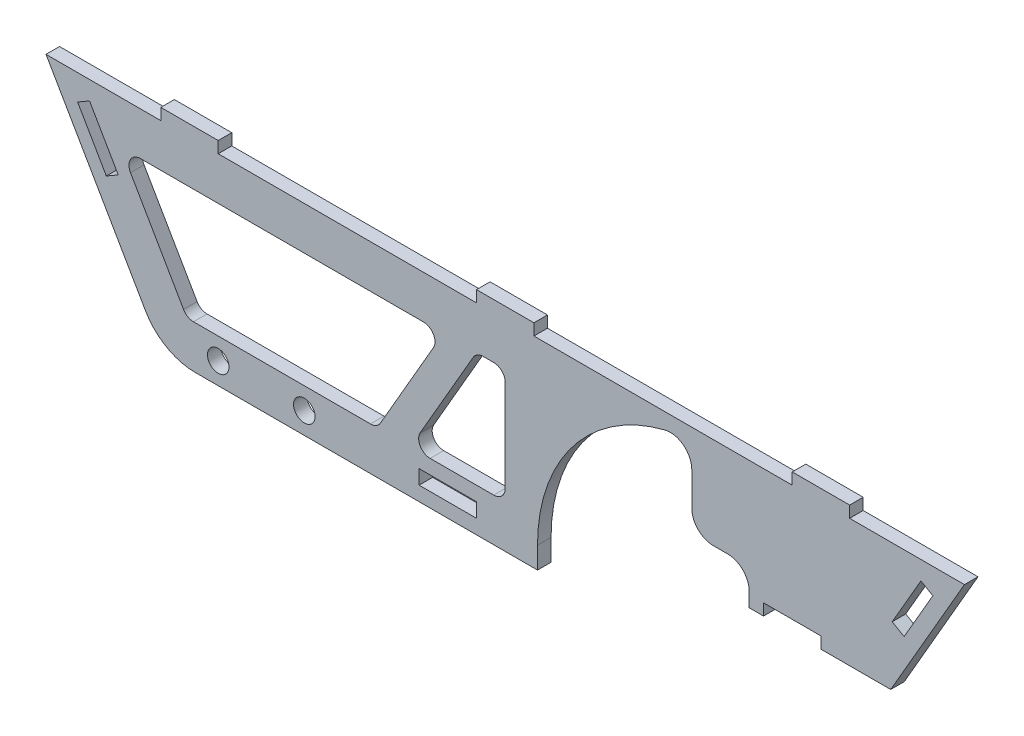
SolidWorks part; units mm, degrees
ref_plane "Front Plane" through (0, 0, 0) normal (0, 0, 1) x (1, 0, 0)
ref_plane "Top Plane" through (0, 0, 0) normal (0, 1, 0) x (1, 0, 0)
ref_plane "Right Plane" through (0, 0, 0) normal (1, 0, 0) x (0, 0, -1)
sketch "Sketch1" plane through (0, 0, 0) normal (0, 0, 1) x (1, 0, 0)
  line L0 (-101.6, 22.225) -> (-75.9368, -22.225)
  line L1 (-101.6, -22.225) -> (-75.9368, -22.225) construction
  line L2 (-101.6, -22.225) -> (-101.6, 22.225) construction
  line L3 (-101.6, 22.225) -> (101.6, 22.225)
  line L4 (101.6, -22.225) -> (101.6, 22.225) construction
  line L5 (-101.6, -22.225) -> (101.6, 22.225) construction
  line L6 (-101.6, 22.225) -> (101.6, -22.225) construction
  line L7 (0, 22.225) -> (0, -25.4) construction
  line L8 (-75.9368, -22.225) -> (101.6, -22.225)
  line L9 (-9.7602, 13.1434) -> (-32.8669, -26.8786) construction
  line L10 (9.7602, 13.1434) -> (32.8669, -26.8786) construction
  line L11 (101.6, 22.225) -> (75.9368, -22.225)
  line L12 (-13.6823, 12.7) -> (-28.347, -12.7)
  line L13 (0, 12.7) -> (0, -12.7)
  line L14 (-6.35, 12.7) -> (-21.0147, -12.7)
  line L15 (-10.4636, 11.9251) -> (-32.8669, -26.8786) construction
  line L16 (-85.1022, 12.7) -> (-70.4375, -12.7)
  line L17 (-85.1022, 12.7) -> (-13.6823, 12.7)
  line L19 (-70.4375, -12.7) -> (-28.347, -12.7)
  line L20 (-21.0147, -12.7) -> (0, -12.7)
  line L21 (-75.9368, -12.7) -> (101.6, -12.7) construction
  line L22 (-85.1022, 12.7) -> (-67.6879, -17.4625) construction
  line L23 (-7.714, 10.3376) -> (-30.1173, -28.4661) construction
  line L26 (85.1022, 12.7) -> (67.6879, -17.4625) construction
  line L28 (-6.35, 12.7) -> (0, 12.7)
  line L29 (-85.1022, 12.7) -> (85.1022, 12.7) construction
  line L30 (-13.2132, 13.5126) -> (-35.6165, -25.2911) construction
  point P0 (0, 0)
  point P16 (7.0106, 11.5559)
  point P17 (30.1173, -28.4661)
  point P20 (13.2132, 13.5126)
  point P21 (35.6165, -25.2911)
  dimension "D1" = 203.2
  dimension "D2" = 44.45
  dimension "D3" = 120
  dimension "D8" = 120
  dimension "D9" = 6.35
  dimension "D4" = 3.175
  dimension "D5" = 3.175
  dimension "D6" = 9.525
  dimension "D7" = 9.525
extrude "Extrude1" add sketch "Sketch1" along normal blind 2.9972
sketch "Sketch2" plane through (0, 0, 2.9972) normal (0, 0, 1) x (1, 0, 0)
  line L0 (-101.6, 22.225) -> (101.6, 22.225) construction
  line L1 (-76.2, 22.225) -> (-63.5, 22.225)
  line L2 (-76.2, 22.225) -> (-76.2, 24.765)
  line L3 (-76.2, 24.765) -> (-63.5, 24.765)
  line L4 (-63.5, 22.225) -> (-63.5, 24.765)
  line L5 (0, 29.6909) -> (0, -12.7) construction
  line L7 (63.5, 22.225) -> (63.5, 24.765)
  line L8 (76.2, 24.765) -> (63.5, 24.765)
  line L9 (76.2, 22.225) -> (76.2, 24.765)
  line L10 (76.2, 22.225) -> (63.5, 22.225)
  line L12 (-6.35, 22.225) -> (6.35, 22.225)
  line L13 (-6.35, 22.225) -> (-6.35, 24.765)
  line L14 (-6.35, 24.765) -> (6.35, 24.765)
  line L15 (6.35, 22.225) -> (6.35, 24.765)
  line L16 (-6.35, 22.225) -> (6.35, 24.765) construction
  line L17 (-6.35, 24.765) -> (6.35, 22.225) construction
  point P14 (0, 23.495)
  dimension "D1" = 12.7
  dimension "D2" = 2.54
  dimension "D3" = 63.5
extrude "Tabs" add sketch "Sketch2" against normal through all
sketch "Sketch3" plane through (0, 0, 2.9972) normal (0, 0, 1) x (1, 0, 0)
  line L0 (-94.6051, 16.5865) -> (-88.2551, 5.588)
  line L1 (-19.05, -19.05) -> (-6.35, -19.05)
  line L2 (-19.05, -19.05) -> (-19.05, -15.875)
  line L3 (-19.05, -15.875) -> (-6.35, -15.875)
  line L4 (-6.35, -19.05) -> (-6.35, -15.875)
  line L5 (-19.05, -19.05) -> (-6.35, -15.875) construction
  line L6 (-19.05, -15.875) -> (-6.35, -19.05) construction
  line L7 (-12.7, -12.7) -> (-12.7, -22.225) construction
  line L9 (-75.9368, -22.225) -> (75.9368, -22.225) construction
  line L10 (-94.6051, 16.5865) -> (-91.9655, 18.1105)
  line L11 (-88.2551, 5.588) -> (-85.6155, 7.112)
  line L12 (-91.9655, 18.1105) -> (-85.6155, 7.112)
  line L13 (-21.0147, -12.7) -> (0, -12.7) construction
  line L14 (-101.6, 22.225) -> (-75.9368, -22.225) construction
  line L15 (-93.2853, 17.3485) -> (-86.9353, 6.35) construction
  line L16 (93.2853, 17.3485) -> (86.9353, 6.35) construction
  line L17 (91.9655, 18.1105) -> (85.6155, 7.112)
  line L18 (88.2551, 5.588) -> (85.6155, 7.112)
  line L19 (94.6051, 16.5865) -> (91.9655, 18.1105)
  line L20 (94.6051, 16.5865) -> (88.2551, 5.588)
  line L21 (57.15, -6.0325) -> (69.85, -6.0325)
  line L22 (57.15, -6.0325) -> (57.15, -3.4925)
  line L23 (57.15, -3.4925) -> (69.85, -3.4925)
  line L24 (69.85, -6.0325) -> (69.85, -3.4925)
  line L25 (57.15, -6.0325) -> (69.85, -3.4925) construction
  line L26 (57.15, -3.4925) -> (69.85, -6.0325) construction
  line L27 (0, 0) -> (0, 28.1268) construction
  point P0 (-12.7, -17.4625)
  point P25 (63.5, -4.7625)
  dimension "D1" = 3.175
  dimension "D2" = 12.7
  dimension "D3" = 12.7
  dimension "D4" = 4.7625
  dimension "D5" = 3.048
  dimension "D6" = 28.575
  dimension "D7" = 12.7
  dimension "D8" = 76.2
  dimension "D9" = 2.54
  dimension "D10" = 12.7
  dimension "D11" = 12.7
extrude "Slots" cut sketch "Sketch3" against normal through all
sketch "Sketch4" plane through (0, 0, 2.9972) normal (0, 0, 1) x (1, 0, 0)
  line L0 (-78.6864, -17.4625) -> (78.6864, -17.4625) construction
  line L1 (-101.6, 22.225) -> (-75.9368, -22.225) construction
  line L2 (101.6, 22.225) -> (75.9368, -22.225) construction
  line L3 (-75.9368, -22.225) -> (75.9368, -22.225) construction
  line L4 (0, -17.4625) -> (0, 0) construction
  circle A0 centre (-63.5, -17.4625) radius 2.3812
  circle A1 centre (-44.45, -17.4625) radius 2.3812
  dimension "D2" = 19.05
  dimension "D3" = 44.45
  dimension "D4" = 4.7625
  dimension "D1" = 4.7625
extrude "Holes" cut sketch "Sketch4" against normal through all
sketch "Sketch5" plane through (0, 0, 2.9972) normal (0, 0, 1) x (1, 0, 0)
  line L0 (41.275, 19.7084) -> (41.275, 1.905)
  line L1 (7.1438, -17.4625) -> (7.1438, -22.225)
  line L2 (-75.9368, -22.225) -> (75.9368, -22.225) construction
  line L3 (7.1438, -22.225) -> (29.3688, -22.225)
  line L4 (53.975, 1.905) -> (53.975, -6.0325)
  line L7 (101.6, 22.225) -> (75.9368, -22.225) construction
  line L8 (-44.45, -17.4625) -> (44.45, -17.4625) construction
  line L9 (41.275, 1.905) -> (53.975, 1.905)
  line L10 (57.15, -6.0325) -> (69.85, -6.0325) construction
  line L11 (53.975, -6.0325) -> (85.2855, -6.0325)
  line L12 (63.5, -3.4925) -> (63.5, -20.3262) construction
  line L13 (29.3688, -22.225) -> (85.2855, -22.225)
  line L14 (85.2855, -6.0325) -> (85.2855, -22.225)
  line L15 (69.85, -3.4925) -> (57.15, -3.4925) construction
  arc A0 (41.275, 19.7084) -> (7.1438, -17.4625) centre (44.45, -17.4625) ccw
  dimension "D5" = 74.6125
  dimension "D1" = 12.7
  dimension "D2" = 22.225
  dimension "D3" = 19.05
  dimension "D4" = 19.05
  dimension "D6" = 7.9375
extrude "Wheel Clearance" cut sketch "Sketch5" against normal through all
fillet "Fillet1" radius 2.54 8 edges at (-21.0147, -12.7, 1.4986) (-6.35, 12.7, 1.4986) (-70.4375, -12.7, 1.4986) (-28.347, -12.7, 1.4986) (-13.6823, 12.7, 1.4986) (-85.1022, 12.7, 1.4986) (0, -12.7, 1.4986) (0, 12.7, 1.4986)
fillet "Fillet2" radius 4.7625 3 edges at (53.975, 1.905, 1.4986) (41.275, 1.905, 1.4986) (41.275, 19.7084, 1.4986)
fillet "Fillet3" radius 12.7 1 edges at (-75.9368, -22.225, 1.4986)
